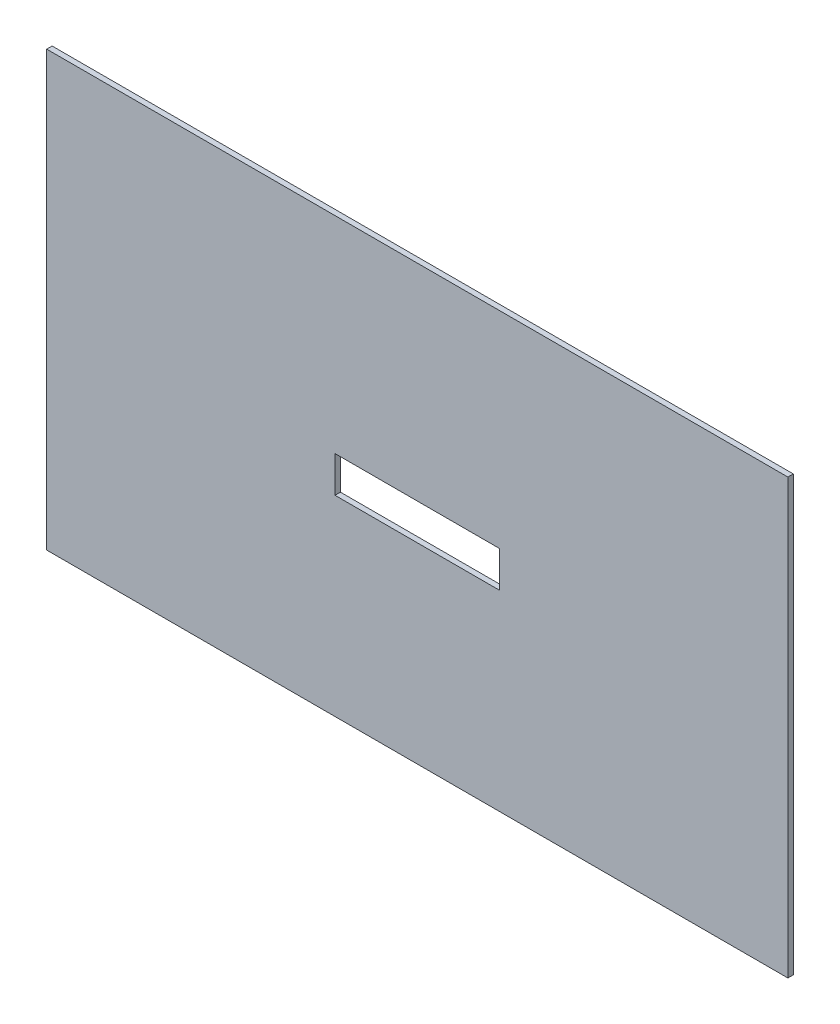
SolidWorks part; units mm, degrees
material "Acrylic (Medium-high impact)"
ref_plane "Front Plane" through (0, 0, 0) normal (0, 0, 1) x (1, 0, 0)
ref_plane "Top Plane" through (0, 0, 0) normal (0, 1, 0) x (1, 0, 0)
ref_plane "Right Plane" through (0, 0, 0) normal (1, 0, 0) x (0, 0, -1)
sketch "Sketch1" plane through (0, 0, 0) normal (0, 0, 1) x (1, 0, 0)
  line L1 (-205, -120) -> (205, -120)
  line L2 (-205, -120) -> (-205, 120)
  line L3 (-205, 120) -> (205, 120)
  line L4 (205, -120) -> (205, 120)
  line L5 (-205, -120) -> (205, 120) construction
  line L6 (-205, 120) -> (205, -120) construction
  point P0 (0, 0)
  dimension "D1" = 240
  dimension "D2" = 410
extrude "Boss-Extrude1" add sketch "Sketch1" along normal mid plane 3
sketch "Sketch2" plane through (0, 0, 1.5) normal (0, 0, 1) x (1, 0, 0)
  line L0 (-205, -120) -> (205, -120) construction
  line L1 (-45.5, -14) -> (45.5, -14)
  line L2 (-45.5, -14) -> (-45.5, 6)
  line L3 (-45.5, 6) -> (45.5, 6)
  line L4 (45.5, -14) -> (45.5, 6)
  line L5 (-45.5, -14) -> (45.5, 6) construction
  line L6 (-45.5, 6) -> (45.5, -14) construction
  point P0 (0, -4)
  dimension "D1" = 91
  dimension "D2" = 106
  dimension "D3" = 20
extrude "Cut-Extrude1" cut sketch "Sketch2" against normal through all
